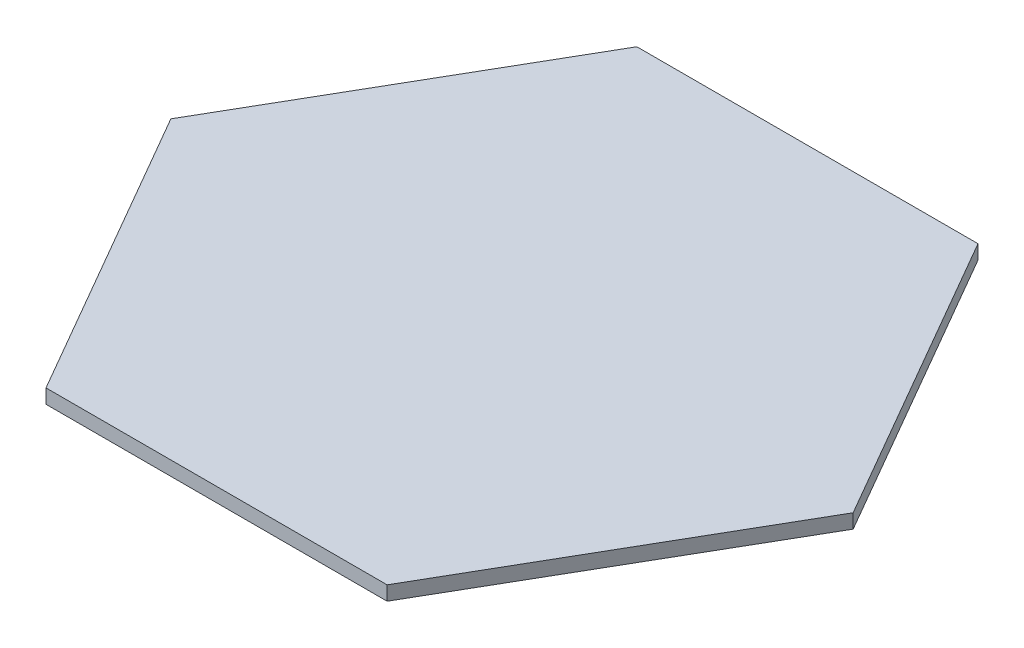
SolidWorks part; units mm, degrees
material "Cedar"
ref_plane "Front Plane" through (0, 0, 0) normal (0, 0, 1) x (1, 0, 0)
ref_plane "Top Plane" through (0, 0, 0) normal (0, 1, 0) x (1, 0, 0)
ref_plane "Right Plane" through (0, 0, 0) normal (1, 0, 0) x (0, 0, -1)
sketch "Sketch1" plane through (0, 0, 0) normal (0, 1, 0) x (1, 0, 0)
  line L0 (0, 0) -> (76.2, 0) construction
  line L1 (76.2, 0) -> (38.1, 65.9911)
  line L2 (38.1, 65.9911) -> (-38.1, 65.9911)
  line L3 (-38.1, 65.9911) -> (-76.2, 0)
  line L4 (-76.2, 0) -> (-38.1, -65.9911)
  line L5 (-38.1, -65.9911) -> (38.1, -65.9911)
  line L6 (38.1, -65.9911) -> (76.2, 0)
  circle A0 centre (0, 0) radius 65.9911 construction
  dimension "D1" = 76.2
extrude "Boss-Extrude1" add sketch "Sketch1" along normal blind 3.175
